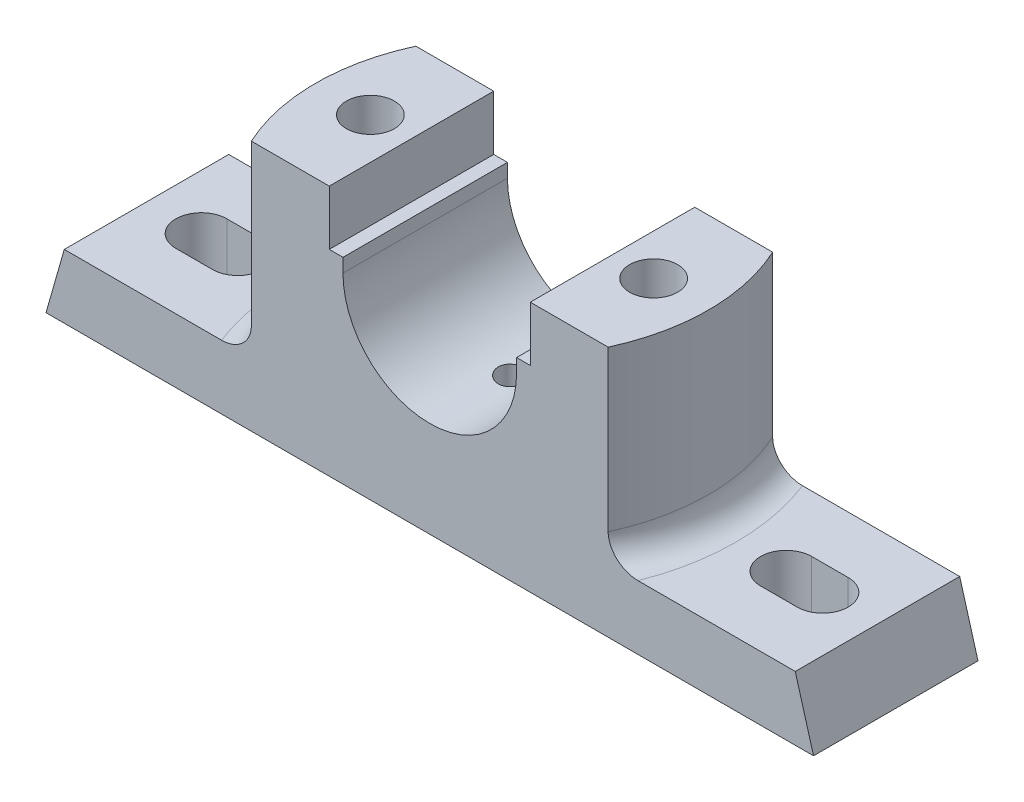
SolidWorks part; units mm, degrees
ref_plane "Front Plane" through (0, 0, 0) normal (0, 0, 1) x (1, 0, 0)
ref_plane "Top Plane" through (0, 0, 0) normal (0, 1, 0) x (1, 0, 0)
ref_plane "Right Plane" through (0, 0, 0) normal (1, 0, 0) x (0, 0, -1)
sketch "Sketch2" plane through (0, 0, 0) normal (0, 0, 1) x (1, 0, 0)
  line L0 (-84, 0) -> (84, 0)
  line L1 (84, 0) -> (80, 14)
  line L2 (80, 14) -> (-80, 14)
  line L3 (-80, 14) -> (-84, 0)
  dimension "D1" = 168
  dimension "D2" = 4
  dimension "D3" = 4
  dimension "D4" = 14
extrude "Boss-Extrude1" add sketch "Sketch2" along normal mid plane 36
sketch "Sketch3" plane through (0, 14, 0) normal (0, 1, 0) x (1, 0, 0)
  line L1 (-39.0512, 18) -> (39.0512, 18)
  line L2 (39.0512, -18) -> (-39.0512, -18)
  line L3 (80, -18) -> (80, 18) construction
  line L4 (-80, 18) -> (80, 18)
  line L5 (-80, -18) -> (80, -18)
  circle A0 centre (0, 0) radius 5.25
  arc A1 (-39.0512, 18) -> (-39.0512, -18) centre (0, 0) ccw
  arc A2 (39.0512, -18) -> (39.0512, 18) centre (0, 0) ccw
  dimension "D1" = 10.5
  dimension "D2" = 86
extrude "Boss-Extrude2" add sketch "Sketch3" along normal blind 41 contours A1 L2 A2 L1
sketch "Sketch4" plane through (0, 14, 0) normal (0, 1, 0) x (1, 0, 0)
  line L0 (-97.4629, 0) -> (97.4629, 0)
  line L1 (60, 0) -> (68, 0) construction
  line L2 (60, 5.5951) -> (68, 5.5951)
  line L3 (60, -5.5951) -> (68, -5.5951)
  line L4 (0, 44.3453) -> (0, -81.7533) construction
  line L5 (-60, 0) -> (-68, 0) construction
  line L6 (-60, 5.5951) -> (-68, 5.5951)
  line L7 (-60, -5.5951) -> (-68, -5.5951)
  arc A0 (60, 5.5951) -> (60, -5.5951) centre (60, 0) ccw
  arc A1 (68, -5.5951) -> (68, 5.5951) centre (68, 0) ccw
  arc A2 (-60, 5.5951) -> (-60, -5.5951) centre (-60, 0) cw
  arc A3 (-68, -5.5951) -> (-68, 5.5951) centre (-68, 0) cw
  point P3 (0, 0)
  point P6 (64, 0)
  point P15 (-64, 0)
  dimension "D1" = 8
  dimension "D2" = 64
extrude "Cut-Extrude1" cut sketch "Sketch4" against normal blind 12 contours L7 A3 L6 A2 | L3 A1 L2 A0
fillet "Fillet1" radius 6 2 edges
sketch "Sketch5" plane through (0, 0, 18) normal (0, 0, 1) x (1, 0, 0)
  line L0 (0, 68.651) -> (0, -34.046) construction
  line L1 (0, 21) -> (29.0986, 21) construction
  line L2 (22, 55) -> (22, 43)
  line L3 (39.0512, 55) -> (-39.0512, 55) construction
  line L4 (22, 43) -> (19, 43)
  line L5 (19, 43) -> (19, 40)
  line L6 (-19, 43) -> (-19, 40)
  line L7 (-22, 43) -> (-19, 43)
  line L8 (-22, 55) -> (-22, 43)
  line L9 (-22, 55) -> (22, 55)
  line L10 (0, 0) -> (28.132, 0) construction
  line L11 (-84, 0) -> (84, 0) construction
  arc A0 (19, 40) -> (-19, 40) centre (0, 40) cw
  dimension "D3" = 22
  dimension "D4" = 19
  dimension "D6" = 21
  dimension "D1" = 3
  dimension "D2" = 12
  dimension "D5" = 3
extrude "Cut-Extrude2" cut sketch "Sketch5" against normal through all
sketch "Sketch7" plane through (0, 55, 0) normal (0, 1, 0) x (1, 0, 0)
  line L0 (-149.0377, 0) -> (151.9478, 0) construction
  line L1 (0, 40.5333) -> (0, -61.5274) construction
  circle A0 centre (31, 0) radius 5.25
  circle A1 centre (-31, 0) radius 5.25
  dimension "D1" = 10.5
  dimension "D2" = 31
extrude "Cut-Extrude3" cut sketch "Sketch7" against normal blind 46
sketch "Sketch10" plane through (0, 0, 0) normal (0, -1, 0) x (1, 0, 0)
  line L0 (-101.6832, 0) -> (101.6832, 0) construction
  line L1 (-84, -18) -> (84, -18) construction
  line L2 (8, 10) -> (76, 10)
  line L3 (8, 10) -> (8, -10)
  line L4 (8, -10) -> (76, -10)
  line L5 (76, 10) -> (76, -10)
  line L6 (8, 10) -> (76, -10) construction
  line L7 (8, -10) -> (76, 10) construction
  line L8 (-84, 18) -> (84, 18) construction
  line L9 (84, 18) -> (84, -18) construction
  line L10 (0, -25.1487) -> (0, 25.1487) construction
  line L11 (-76, 10) -> (-76, -10)
  line L12 (-8, 10) -> (-76, 10)
  line L13 (-8, 10) -> (-8, -10)
  line L14 (-8, -10) -> (-76, -10)
  point P2 (42, 0)
  point P16 (0, 0)
  dimension "D1" = 8
  dimension "D2" = 8
  dimension "D3" = 8
  dimension "D4" = 8
extrude "Cut-Extrude4" cut sketch "Sketch10" against normal blind 2
fillet "Fillet2" radius 1 4 edges at (-8, 2, 0) (-76, 2, 0) (8, 2, 0) (76, 2, 0)
sketch "Sketch11" plane through (0, 0, 0) normal (0, -1, 0) x (1, 0, 0)
  line L0 (0, 34.112) -> (0, -41.512) construction
  line L1 (-21, -10) -> (-41, 10) construction
  line L2 (21, 10) -> (41, 10)
  line L3 (21, 10) -> (21, -10)
  line L4 (21, -10) -> (41, -10)
  line L5 (41, 10) -> (41, -10)
  line L6 (21, 10) -> (41, -10) construction
  line L7 (21, -10) -> (41, 10) construction
  line L8 (-21, 10) -> (-41, -10) construction
  line L9 (-41, 10) -> (-41, -10)
  line L10 (-21, -10) -> (-41, -10)
  line L11 (-21, 10) -> (-21, -10)
  line L12 (-21, 10) -> (-41, 10)
  point P3 (31, 0)
  point P12 (-31, 0)
  dimension "D1" = 31
extrude "Cut-Extrude5" cut sketch "Sketch11" against normal blind 9
ref_plane "Plane2" through (0, 25, 0) normal (0, -1, 0) x (-1, 0, 0)
sketch "Sketch15" plane through (0, 25, 0) normal (0, -1, 0) x (-1, 0, 0)
  circle A0 centre (0, 0) radius 3
  dimension "D1" = 6
extrude "Cut-Extrude6" cut sketch "Sketch15" along normal blind 10
